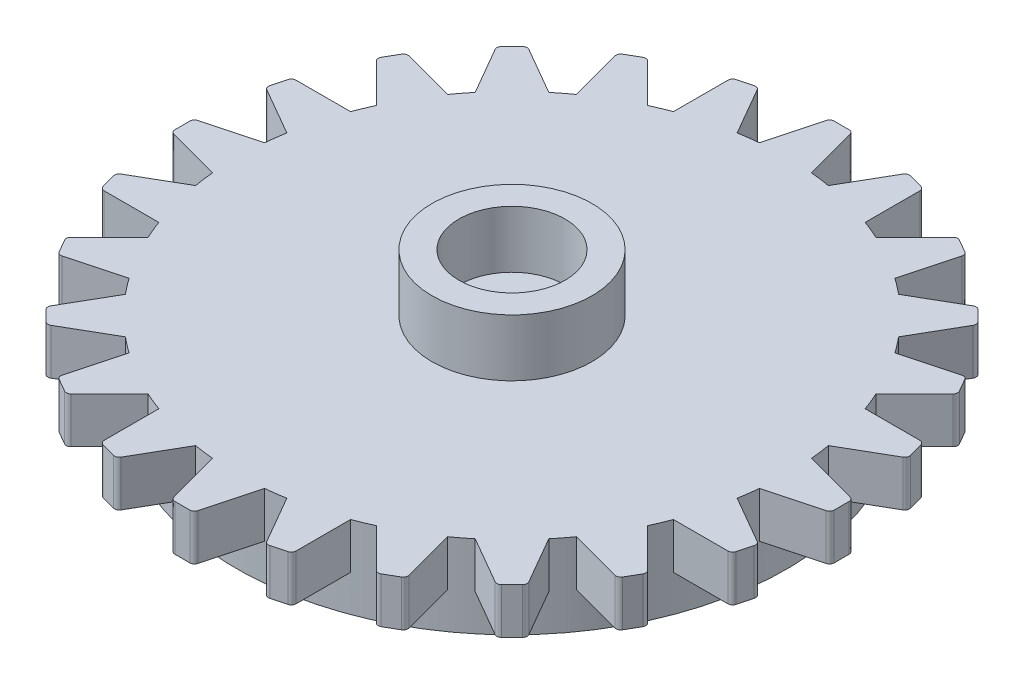
SolidWorks part; units mm, degrees
material "ABS"
ref_plane "Front Plane" through (0, 0, 0) normal (0, 0, 1) x (1, 0, 0)
ref_plane "Top Plane" through (0, 0, 0) normal (0, 1, 0) x (1, 0, 0)
ref_plane "Right Plane" through (0, 0, 0) normal (1, 0, 0) x (0, 0, -1)
sketch "Sketch1" plane through (0, 0, 0) normal (0, 1, 0) x (1, 0, 0)
  circle A0 centre (0, 0) radius 15
  dimension "D1" = 30
extrude "Boss-Extrude1" add sketch "Sketch1" along normal blind 2.5
sketch "Sketch2" plane through (0, 2.5, 0) normal (0, 1, 0) x (1, 0, 0)
  circle A0 centre (0, 0) radius 4.37
  circle A1 centre (0, 0) radius 2.9
  dimension "D1" = 8.74
  dimension "D2" = 5.8
extrude "Boss-Extrude2" add sketch "Sketch2" along normal blind 3.12
sketch "Sketch3" plane through (0, 0, 0) normal (0, -1, 0) x (1, 0, 0)
  line L0 (0, 0) -> (0, 21.4338) construction
  line L1 (0, 18) -> (0.6, 18)
  line L2 (0.6, 18) -> (1.5646, 14.4)
  line L3 (1.5646, 14.4) -> (-1.5646, 14.4)
  line L4 (-1.5646, 14.4) -> (-0.6, 18)
  line L5 (-0.6, 18) -> (0, 18)
  line L6 (-0.6, 18) -> (-6.2955, 18) construction
  line L7 (0.6, 18) -> (6.2539, 18) construction
  dimension "D1" = 14.4
  dimension "D2" = 18
  dimension "D3" = 0.6
  dimension "D4" = 0.6
  dimension "D5" = 75
  dimension "D6" = 75
extrude "Boss-Extrude3" add sketch "Sketch3" against normal blind 2.5 contours L2 L3 L4 L5 L1
fillet "Fillet1" radius 0.25 2 edges at (0.6, 1.25, 18) (-0.6, 1.25, 18)
pattern_circular "CirPattern1" count 24 over 360 about axis through (0, 0, 0) along (0, 1, 0) of "Boss-Extrude3", "Fillet1"
sketch "Sketch4" plane through (0, 0, 0) normal (0, -1, 0) x (1, 0, 0)
  circle A0 centre (0, 0) radius 15
  circle A1 centre (0, 0) radius 12
extrude "Boss-Extrude4" add sketch "Sketch4" along normal blind 2
